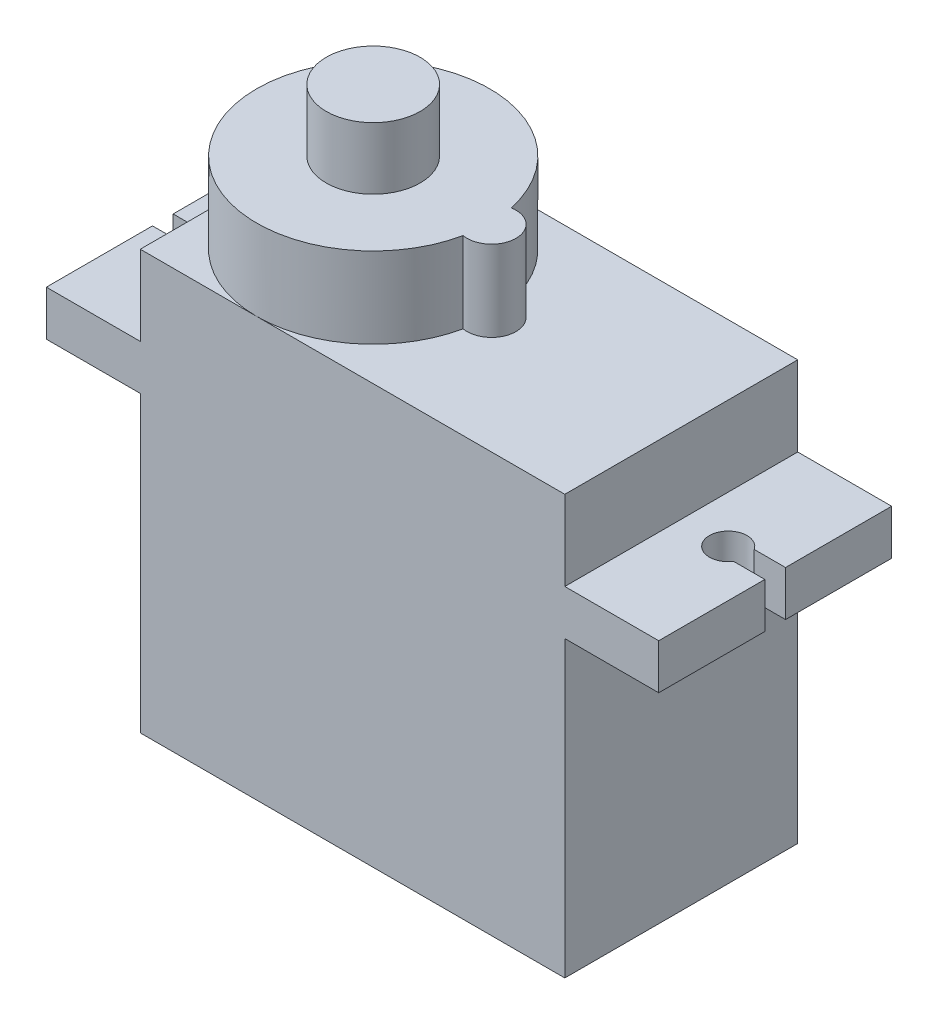
SolidWorks part; units mm, degrees
ref_plane "Front Plane" through (0, 0, 0) normal (0, 0, 1) x (1, 0, 0)
ref_plane "Top Plane" through (0, 0, 0) normal (0, 1, 0) x (1, 0, 0)
ref_plane "Right Plane" through (0, 0, 0) normal (1, 0, 0) x (0, 0, -1)
sketch "Sketch1" plane through (0, 0, 0) normal (0, 1, 0) x (1, 0, 0)
  line L1 (-11.3, -6.2) -> (11.3, -6.2)
  line L2 (-11.3, -6.2) -> (-11.3, 6.2)
  line L3 (-11.3, 6.2) -> (11.3, 6.2)
  line L4 (11.3, -6.2) -> (11.3, 6.2)
  line L5 (-11.3, -6.2) -> (11.3, 6.2) construction
  line L6 (-11.3, 6.2) -> (11.3, -6.2) construction
  point P0 (0, 0)
  dimension "D1" = 22.6
  dimension "D2" = 12.4
extrude "Boss-Extrude1" add sketch "Sketch1" along normal blind 22.3
sketch "Sketch2" plane through (11.3, 0, 0) normal (1, 0, 0) x (0, 0, -1)
  line L0 (-6.2, 22.3) -> (-6.2, 0) construction
  line L1 (-6.2, 18.05) -> (6.2, 18.05)
  line L2 (-6.2, 18.05) -> (-6.2, 15.65)
  line L3 (-6.2, 15.65) -> (6.2, 15.65)
  line L4 (6.2, 18.05) -> (6.2, 15.65)
  line L5 (6.2, 22.3) -> (6.2, 0) construction
  line L6 (-6.2, 22.3) -> (6.2, 22.3) construction
  dimension "D1" = 4.25
  dimension "D2" = 2.4
extrude "Boss-Extrude2" add sketch "Sketch2" along normal blind 5
sketch "Sketch3" plane through (-11.3, 0, 0) normal (-1, 0, 0) x (0, 0, 1)
  line L4 (6.2, 15.65) -> (6.2, 18.05)
  line L5 (-6.2, 15.65) -> (6.2, 15.65)
  line L6 (-6.2, 18.05) -> (-6.2, 15.65)
  line L7 (6.2, 18.05) -> (-6.2, 18.05)
  line L8 (6.2, 15.65) -> (6.2, 18.05)
  line L9 (-6.2, 15.65) -> (6.2, 15.65)
  line L10 (-6.2, 18.05) -> (-6.2, 15.65)
  line L11 (6.2, 18.05) -> (-6.2, 18.05)
  dimension "D1" = 0
extrude "Boss-Extrude3" add sketch "Sketch3" along normal blind 5
sketch "Sketch4" plane through (0, 18.05, 0) normal (0, 1, 0) x (1, 0, 0)
  line L0 (-16.3, -6.2) -> (-16.3, 6.2) construction
  line L1 (16.3, 6.2) -> (16.3, -6.2) construction
  line L3 (-16.3, 0.55) -> (-14.6352, 0.55)
  line L4 (-16.3, 0.55) -> (-16.3, -0.55)
  line L5 (-16.3, -0.55) -> (-14.6352, -0.55)
  line L7 (16.3, -0.55) -> (14.6352, -0.55)
  line L8 (16.3, -0.55) -> (16.3, 0.55)
  line L9 (16.3, 0.55) -> (14.6352, 0.55)
  arc A0 (-14.6352, -0.55) -> (-14.6352, 0.55) centre (-13.8, 0) ccw
  arc A1 (14.6352, 0.55) -> (14.6352, -0.55) centre (13.8, 0) ccw
  dimension "D1" = 2
  dimension "D2" = 2
  dimension "D4" = 2.5
  dimension "D3" = 2.5
  dimension "D5" = 1.1
  dimension "D6" = 0.55
  dimension "D7" = 1.1
  dimension "D8" = 0.55
extrude "Cut-Extrude1" cut sketch "Sketch4" against normal up to next
sketch "Sketch5" plane through (0, 18.05, 0) normal (0, 1, 0) x (1, 0, 0)
  line L0 (16.3, 6.2) -> (16.3, 0.55) construction
  line L1 (14.6352, 0.55) -> (16.3, 0.55)
  line L3 (14.6352, -0.55) -> (16.3, -0.55)
  line L4 (16.3, 0.55) -> (16.3, -0.55)
  arc A0 (14.6352, 0.55) -> (14.6352, -0.55) centre (13.8, 0) ccw
  dimension "D1" = 2
  dimension "D2" = 1.1
  dimension "D3" = 0.55
  dimension "D4" = 2.5
extrude "Cut-Extrude2" [suppressed] cut sketch "Sketch5" against normal up to next contours L1 L4 L3 A0
sketch "Sketch6" plane through (0, 22.3, 0) normal (0, 1, 0) x (1, 0, 0)
  line L0 (-11.3, 6.2) -> (-11.3, -6.2) construction
  line L1 (1.2, 1.3) -> (0.9622, 1.3)
  line L2 (1.2, -1.3) -> (0.9622, -1.3)
  arc A0 (0.9667, 1.2789) -> (0.9667, -1.2789) centre (-5.1, 0) ccw
  arc A1 (0.9667, -1.2789) -> (0.9667, 1.2789) centre (1.2, 0) ccw
  dimension "D2" = 12.4
  dimension "D3" = 2.6
  dimension "D1" = 6.2
  dimension "D4" = 6.3
extrude "Boss-Extrude4" add sketch "Sketch6" along normal blind 4.3 contours A1 A0
sketch "Sketch7" plane through (0, 26.6, 0) normal (0, 1, 0) x (1, 0, 0)
  circle A0 centre (-5.1, 0) radius 2.5
  dimension "D1" = 5
extrude "Boss-Extrude5" add sketch "Sketch7" along normal blind 3.3
sketch "Sketch8" plane through (-11.3, 0, 0) normal (-1, 0, 0) x (0, 0, 1)
  line L0 (-6.2, 0) -> (6.2, 0) construction
  circle A0 centre (-1.2, 4.5) radius 0.6
  circle A1 centre (0, 4.5) radius 0.6
  circle A2 centre (1.2, 4.5) radius 0.6
  dimension "D1" = 4.5
  dimension "D2" = 1.2
  dimension "D3" = 1.2
  dimension "D4" = 1.2
extrude "Boss-Extrude7" add sketch "Sketch8" along normal blind 2.3 separate body contours A1 | A0 | A2
ref_plane "Plane1" through (0, 18.05, 0) normal (0, 1, 0) x (1, 0, 0)
inserted part "Microservo horn" [suppressed]
move or copy body "Body-Move/Copy1" [suppressed] bodies to move or copy 111 placed by mates yes
combine bodies "Combine1" [suppressed] operation type add bodies to combine 107 112
